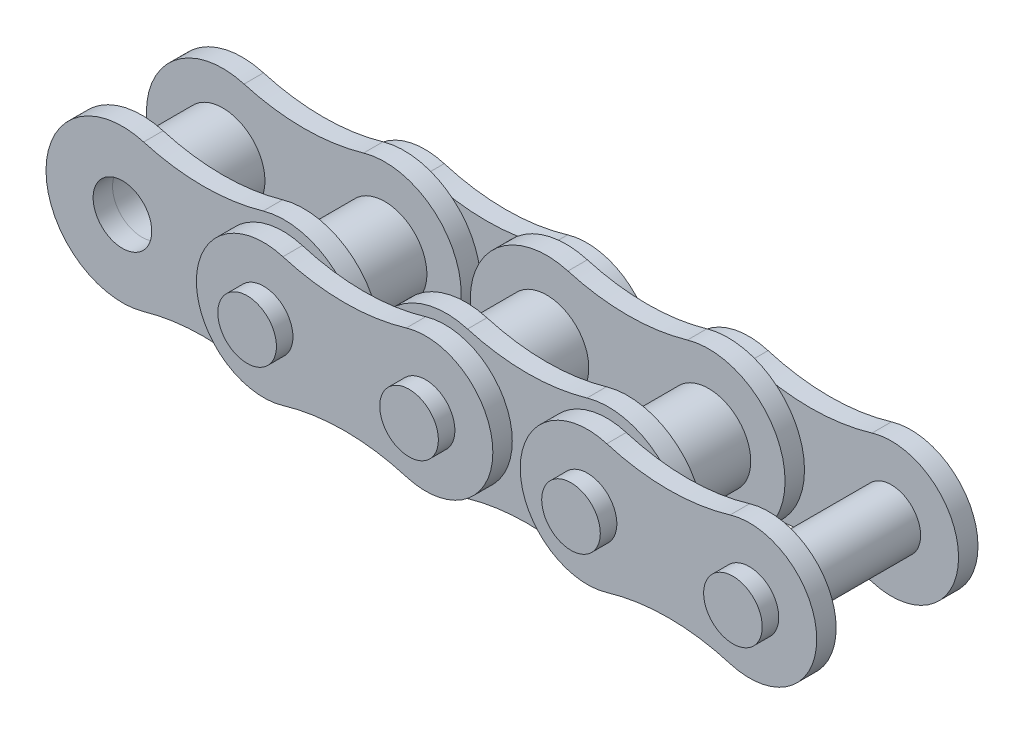
SolidWorks part; units mm, degrees
ref_plane "Front Plane" through (0, 0, 0) normal (0, 0, 1) x (1, 0, 0)
ref_plane "Top Plane" through (0, 0, 0) normal (0, 1, 0) x (1, 0, 0)
ref_plane "Right Plane" through (0, 0, 0) normal (1, 0, 0) x (0, 0, -1)
sketch "Sketch1" plane through (0, 0, 0) normal (0, 0, 1) x (1, 0, 0)
  line L0 (-3.175, 0) -> (3.175, 0) construction
  line L1 (-3.175, 2.9972) -> (-3.175, -2.9972) construction
  line L2 (0, -2.5476) -> (0, 2.5476) construction
  circle A0 centre (-3.175, 0) radius 1.651
  circle A1 centre (3.175, 0) radius 1.651
  circle A2 centre (-3.175, 0) radius 1.1493
  circle A3 centre (3.175, 0) radius 1.1493
  arc A4 (-2.3429, 2.8794) -> (-2.3429, -2.8794) centre (-3.175, 0) ccw
  arc A5 (2.3429, -2.8794) -> (2.3429, 2.8794) centre (3.175, 0) ccw
  arc A6 (-2.3429, 2.8794) -> (2.3429, 2.8794) centre (0, 10.9864) ccw
  arc A7 (-2.3429, -2.8794) -> (2.3429, -2.8794) centre (0, -10.9864) cw
  dimension "Roller Dia" = 3.302
  dimension "Pin Dia" = 2.2987
  dimension "Pitch" = 6.35
  dimension "H" = 5.9944
  dimension "D2" = 5.0952
sketch "Sketch2" plane through (0, 0, 0) normal (0, 1, 0) x (1, 0, 0)
  line L0 (0, 1.5875) -> (0, -1.5875) construction
  point P2 (0, -2.3495)
  point P4 (0, 2.3495)
  point P5 (0, 2.4003)
  point P6 (0, 3.1623)
  dimension "W" = 3.175
  dimension "T" = 0.762
  dimension "D1" = 0.762
  dimension "D2" = 0.762
  dimension "D3" = 0.0508
ref_plane "Plane1" through (0, 0, 1.5875) normal (0, 0, 1) x (1, 0, 0)
ref_plane "Plane2" through (0, 0, -2.4003) normal (0, 0, 1) x (1, 0, 0)
sketch "Sketch4" plane through (0, 0, 0) normal (0, 0, 1) x (1, 0, 0)
  circle A0 centre (-3.175, 0) radius 1.651 construction
  circle A1 centre (-3.175, 0) radius 1.651
  circle A2 centre (3.175, 0) radius 1.651 construction
  circle A3 centre (3.175, 0) radius 1.651
  circle A4 centre (-3.175, 0) radius 1.1747
  circle A5 centre (3.175, 0) radius 1.1747
  dimension "D1" = 2.3495
  dimension "D2" = 2.3495
extrude "Boss-Extrude1" add sketch "Sketch4" along normal mid plane 3.175
sketch "Sketch5" plane through (0, 0, 1.5875) normal (0, 0, 1) x (1, 0, 0)
  arc A0 (-2.3429, 2.8794) -> (-2.3429, -2.8794) centre (-3.175, 0) ccw construction
  arc A1 (-2.3429, 2.8794) -> (2.3429, 2.8794) centre (0, 10.9864) ccw construction
  circle A2 centre (-3.175, 0) radius 1.1493 construction
  arc A3 (2.3429, -2.8794) -> (2.3429, 2.8794) centre (3.175, 0) ccw construction
  circle A4 centre (3.175, 0) radius 1.1493 construction
  arc A5 (2.3429, -2.8794) -> (-2.3429, -2.8794) centre (0, -10.9864) ccw construction
  arc A6 (-2.3429, 2.8794) -> (-2.3429, -2.8794) centre (-3.175, 0) ccw
  arc A7 (-2.3429, 2.8794) -> (2.3429, 2.8794) centre (0, 10.9864) ccw
  circle A8 centre (-3.175, 0) radius 1.1493
  arc A9 (2.3429, -2.8794) -> (2.3429, 2.8794) centre (3.175, 0) ccw
  circle A10 centre (3.175, 0) radius 1.1493
  arc A11 (2.3429, -2.8794) -> (-2.3429, -2.8794) centre (0, -10.9864) ccw
extrude "Boss-Extrude2" add sketch "Sketch5" along normal up to vertex (0.762 mm away) separate body up to point (0, 0, 2.3495)
pattern_linear "LPattern1" count 2 spacing 6.35 along (1, 0, 0) of bodies 102
sketch "Sketch7" plane through (0, 0, -2.4003) normal (0, 0, 1) x (1, 0, 0)
  line L0 (9.525, 2.6375) -> (9.525, -2.6375) construction
  arc A0 (3.931, 2.5269) -> (3.931, -2.5269) centre (3.175, 0) ccw
  arc A1 (8.769, -2.5269) -> (8.769, 2.5269) centre (9.525, 0) ccw
  arc A2 (2.3429, -2.8794) -> (2.3429, 2.8794) centre (3.175, 0) ccw construction
  circle A3 centre (9.525, 0) radius 1.651 construction
  arc A4 (3.931, 2.5269) -> (8.769, 2.5269) centre (6.35, 10.6115) ccw
  arc A5 (3.931, -2.5269) -> (8.769, -2.5269) centre (6.35, -10.6115) cw
  arc A6 (-2.3429, 2.8794) -> (2.3429, 2.8794) centre (0, 10.9864) ccw construction
  circle A7 centre (3.175, 0) radius 1.1493 construction
  circle A8 centre (3.175, 0) radius 1.1493
  circle A9 centre (9.525, 0) radius 1.1493
  dimension "D2" = 5.2751
extrude "Boss-Extrude3" add sketch "Sketch7" against normal up to vertex (0.762 mm away) separate body up to point (0, 0, -3.1623)
mirror "Mirror1" about plane through (0, 0, 0) normal (0, 0, 1) of bodies 103 105
sketch "Sketch8" plane through (0, 0, 0) normal (0, 0, 1) x (1, 0, 0)
  circle A0 centre (3.175, 0) radius 1.1493
  circle A1 centre (9.525, 0) radius 1.1493
  circle A2 centre (3.175, 0) radius 1.1493 construction
  circle A3 centre (9.525, 0) radius 1.1494 construction
extrude "Boss-Extrude4" add sketch "Sketch8" against normal blind 3.81 and the other way blind 3.81 separate body
pattern_linear "LPattern2" count 2 spacing 12.7 along (1, 0, 0) of bodies 109 108 107 106 105 104 103 102 101
delete or keep bodies "Body-Delete1" type delete bodies bodies 115
combine bodies "Combine1" operation type add bodies to combine 102 103 104 105 106 107 108 109 110 111 112 113 114 116 117 118 101
sketch "Sketch9" plane through (0, 0, 0) normal (0, 0, 1) x (1, 0, 0)
  line L0 (22.225, 2.6375) -> (22.225, -2.6375) construction
  line L1 (15.875, 2.9972) -> (15.875, -2.9972) construction
  arc A0 (15.0429, -2.8794) -> (15.0429, 2.8794) centre (15.875, 0) ccw construction
  arc A1 (15.875, -2.9972) -> (15.875, 2.9972) centre (15.875, 0) ccw
  arc A2 (21.469, -2.5269) -> (21.469, 2.5269) centre (22.225, 0) ccw construction
  arc A3 (22.225, -2.6375) -> (22.225, 2.6375) centre (22.225, 0) ccw
  circle A4 centre (-3.175, 0) radius 1.651 construction
  circle A5 centre (-3.175, 0) radius 1.651
equation "\"D2@Sketch1\" =\"H@Sketch1\"*.85"
equation "\"D1@Sketch2\" = \"T@Sketch2\""
equation "\"D1@Sketch4\" = \"Pin Dia@Sketch1\"+.002"
equation "\"D2@Sketch4\" = \"D1@Sketch4\""
equation "\"D1@Boss-Extrude1\" = \"W@Sketch2\""
equation "\"D2@Sketch2\" = \"T@Sketch2\""
equation "\"D3@LPattern1\" = \"Pitch@Sketch1\""
equation "\"D3@LPattern2\" = \"Pitch@Sketch1\"*2"
equation "\"D2@Sketch7\" = \"H@Sketch1\"*.88"
